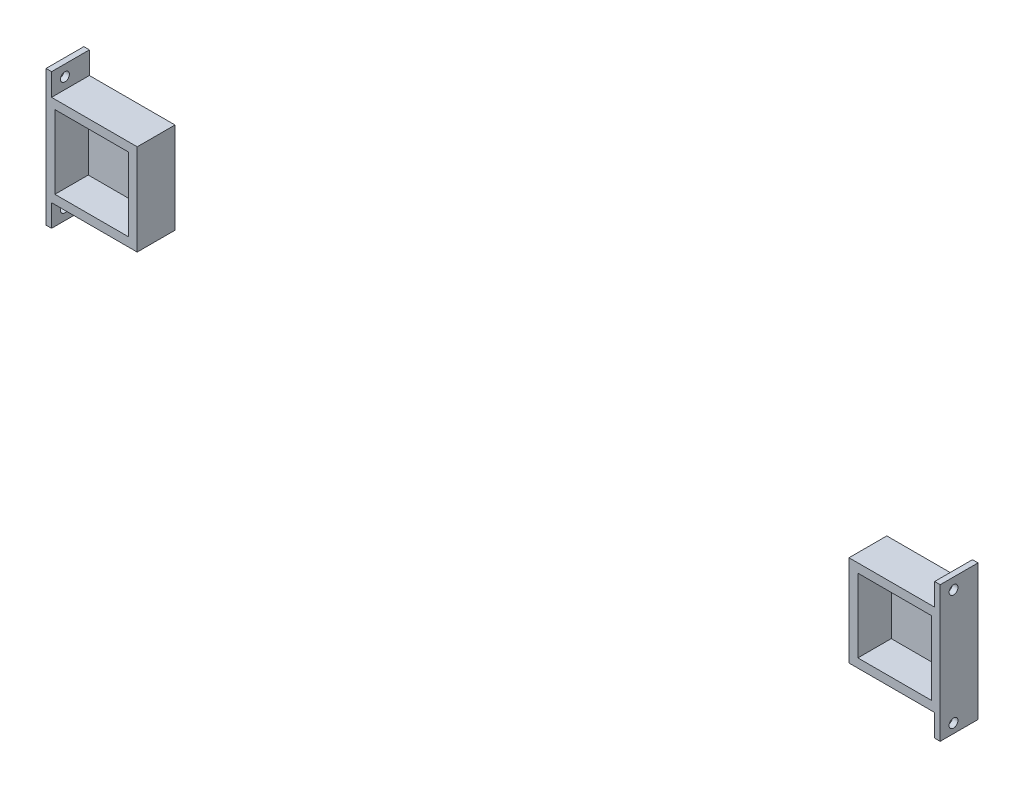
SolidWorks part; units mm, degrees
ref_plane "Front Plane" through (0, 0, 0) normal (0, 0, 1) x (1, 0, 0)
ref_plane "Top Plane" through (0, 0, 0) normal (0, 1, 0) x (1, 0, 0)
ref_plane "Right Plane" through (0, 0, 0) normal (1, 0, 0) x (0, 0, -1)
sketch "Sketch1" plane through (0, 0, 0) normal (0, 0, 1) x (1, 0, 0)
  line L1 (0, 0) -> (41.91, 0)
  line L2 (0, 0) -> (0, 41.91)
  line L3 (0, 41.91) -> (41.91, 41.91)
  line L4 (41.91, 0) -> (41.91, 41.91)
  line L5 (-5.08, 46.99) -> (46.99, 46.99)
  line L6 (-5.08, 46.99) -> (-5.08, -5.08)
  line L7 (-5.08, -5.08) -> (46.99, -5.08)
  line L8 (46.99, 46.99) -> (46.99, -5.08)
  line L9 (458.47, 41.91) -> (500.38, 41.91)
  line L10 (458.47, 41.91) -> (458.47, 0)
  line L11 (458.47, 0) -> (500.38, 0)
  line L12 (500.38, 41.91) -> (500.38, 0)
  line L13 (453.39, 46.99) -> (505.46, 46.99)
  line L14 (453.39, 46.99) -> (453.39, -5.08)
  line L15 (453.39, -5.08) -> (505.46, -5.08)
  line L16 (505.46, 46.99) -> (505.46, -5.08)
  point P17 (458.47, 20.955)
  dimension "D1" = 41.91
  dimension "D2" = 41.91
  dimension "D3" = 5.08
  dimension "D4" = 5.08
  dimension "D5" = 5.08
  dimension "D6" = 5.08
  dimension "D7" = 41.91
  dimension "D8" = 41.91
  dimension "D9" = 5.08
  dimension "D10" = 5.08
  dimension "D11" = 406.4
extrude "Boss-Extrude1" add sketch "Sketch1" along normal blind 19.05
sketch "Sketch2" plane through (0, 0, 0) normal (0, 0, -1) x (-1, 0, 0)
  line L0 (-46.99, 46.99) -> (5.08, 46.99) construction
  line L10 (-8.255, -5.08) -> (-8.255, -208.28)
  line L11 (-8.255, -208.28) -> (-33.655, -208.28)
  line L12 (-33.655, -5.08) -> (-33.655, -182.88)
  line L15 (-365.125, -208.28) -> (-390.525, -208.28)
  line L25 (-33.655, -208.28) -> (-365.125, -208.28)
  line L27 (-33.655, -182.88) -> (-365.125, -182.88)
  line L34 (-8.255, 46.99) -> (-8.255, 173.99)
  line L35 (-8.255, 173.99) -> (-33.655, 173.99)
  line L37 (-46.99, -5.08) -> (-46.99, 46.99) construction
  line L40 (-365.125, 173.99) -> (-391.5985, 173.99)
  line L54 (-33.655, 173.99) -> (-365.125, 173.99)
  line L55 (-33.655, 46.99) -> (-33.655, 148.59)
  line L56 (-33.655, 148.59) -> (-33.655, 46.99)
  line L57 (-466.725, 46.99) -> (-466.725, 148.59)
  line L58 (-365.125, 148.59) -> (-33.655, 148.59)
  line L59 (-505.46, 46.99) -> (-453.39, 46.99) construction
  line L61 (-8.255, 46.99) -> (-33.655, 46.99)
  line L62 (-8.255, -5.08) -> (-33.655, -5.08)
  line L63 (5.08, -5.08) -> (-46.99, -5.08) construction
  line L64 (-466.725, 148.59) -> (-365.125, 148.59)
  line L65 (-453.39, 46.99) -> (-453.39, -5.08) construction
  line L67 (-492.125, 46.99) -> (-492.125, 173.99)
  line L68 (-492.125, 173.99) -> (-391.5985, 173.99)
  line L69 (-466.725, 46.99) -> (-492.125, 46.99)
  line L70 (-466.725, -5.08) -> (-466.725, -182.88)
  line L71 (-453.39, -5.08) -> (-505.46, -5.08) construction
  line L72 (-466.725, -182.88) -> (-365.125, -182.88)
  line L73 (-492.125, -5.08) -> (-492.125, -208.28)
  line L74 (-492.125, -208.28) -> (-390.525, -208.28)
  line L75 (-466.725, -5.08) -> (-492.125, -5.08)
  dimension "D1" = 203.2
  dimension "D2" = 25.4
  dimension "D3" = 127
  dimension "D4" = 25.4
  dimension "D5" = 13.335
  dimension "D6" = 101.6
  dimension "D7" = 0
  dimension "D8" = 25.4
  dimension "D9" = 25.4
  dimension "D10" = 331.47
  dimension "D11" = 127
  dimension "D12" = 25.4
  dimension "D13" = 13.335
sketch "Sketch3" plane through (0, 0, 0) normal (0, 0, -1) x (-1, 0, 0)
  line L1 (5.08, -5.08) -> (-46.99, -5.08)
  line L2 (5.08, -5.08) -> (5.08, 46.99)
  line L3 (5.08, 46.99) -> (-46.99, 46.99)
  line L4 (-46.99, -5.08) -> (-46.99, 46.99)
  line L5 (-453.39, -5.08) -> (-505.46, -5.08)
  line L6 (-453.39, -5.08) -> (-453.39, 46.99)
  line L7 (-453.39, 46.99) -> (-505.46, 46.99)
  line L8 (-505.46, -5.08) -> (-505.46, 46.99)
extrude "Boss-Extrude6" add sketch "Sketch3" along normal blind 2.54
sketch "Sketch4" plane through (-5.08, 0, 0) normal (-1, 0, 0) x (0, 0, 1)
  line L0 (19.05, 46.99) -> (-2.54, 46.99) construction
  line L1 (19.05, -5.08) -> (-2.54, -5.08)
  line L2 (19.05, -5.08) -> (19.05, -17.78)
  line L3 (19.05, -17.78) -> (-2.54, -17.78)
  line L4 (-2.54, -5.08) -> (-2.54, -17.78)
  line L5 (19.05, -5.08) -> (-2.54, -17.78) construction
  line L6 (19.05, -17.78) -> (-2.54, -5.08) construction
  line L7 (19.05, 46.99) -> (-2.54, 46.99)
  line L8 (19.05, 46.99) -> (19.05, 59.69)
  line L9 (19.05, 59.69) -> (-2.54, 59.69)
  line L10 (-2.54, 46.99) -> (-2.54, 59.69)
  line L11 (19.05, 46.99) -> (-2.54, 59.69) construction
  line L12 (19.05, 59.69) -> (-2.54, 46.99) construction
  line L13 (19.05, 46.99) -> (19.05, -5.08) construction
  line L14 (-2.54, -5.08) -> (-2.54, 46.99) construction
  circle A2 centre (11.43, 53.34) radius 2.54
  circle A3 centre (11.43, -11.43) radius 2.54
  point P4 (8.255, -11.43)
  point P10 (8.255, 53.34)
  dimension "D5" = 5.08
  dimension "D6" = 7.62
  dimension "D7" = 5.08
  dimension "D1" = 0
  dimension "D2" = 0
  dimension "D3" = 12.7
  dimension "D4" = 12.7
  dimension "D8" = 7.62
extrude "Boss-Extrude7" add sketch "Sketch4" against normal blind 3.175
sketch "Sketch5" plane through (505.46, 0, 0) normal (1, 0, 0) x (0, 0, -1)
  line L1 (-19.05, -5.08) -> (2.54, -5.08)
  line L2 (-19.05, -5.08) -> (-19.05, -17.78)
  line L3 (-19.05, -17.78) -> (2.54, -17.78)
  line L4 (2.54, -5.08) -> (2.54, -17.78)
  line L5 (-19.05, -5.08) -> (2.54, -17.78) construction
  line L6 (-19.05, -17.78) -> (2.54, -5.08) construction
  line L7 (-19.05, 46.99) -> (2.54, 46.99)
  line L8 (-19.05, 46.99) -> (-19.05, 59.69)
  line L9 (-19.05, 59.69) -> (2.54, 59.69)
  line L10 (2.54, 46.99) -> (2.54, 59.69)
  line L11 (-19.05, 46.99) -> (2.54, 59.69) construction
  line L12 (-19.05, 59.69) -> (2.54, 46.99) construction
  circle A2 centre (-11.43, -12.5092) radius 2.54
  circle A3 centre (-11.43, 53.34) radius 2.54
  point P4 (-8.255, -11.43)
  point P11 (-8.255, 53.34)
  dimension "D1" = 5.08
  dimension "D4" = 5.08
  dimension "D2" = 7.62
  dimension "D3" = 7.62
extrude "Boss-Extrude8" add sketch "Sketch5" against normal blind 3.175
